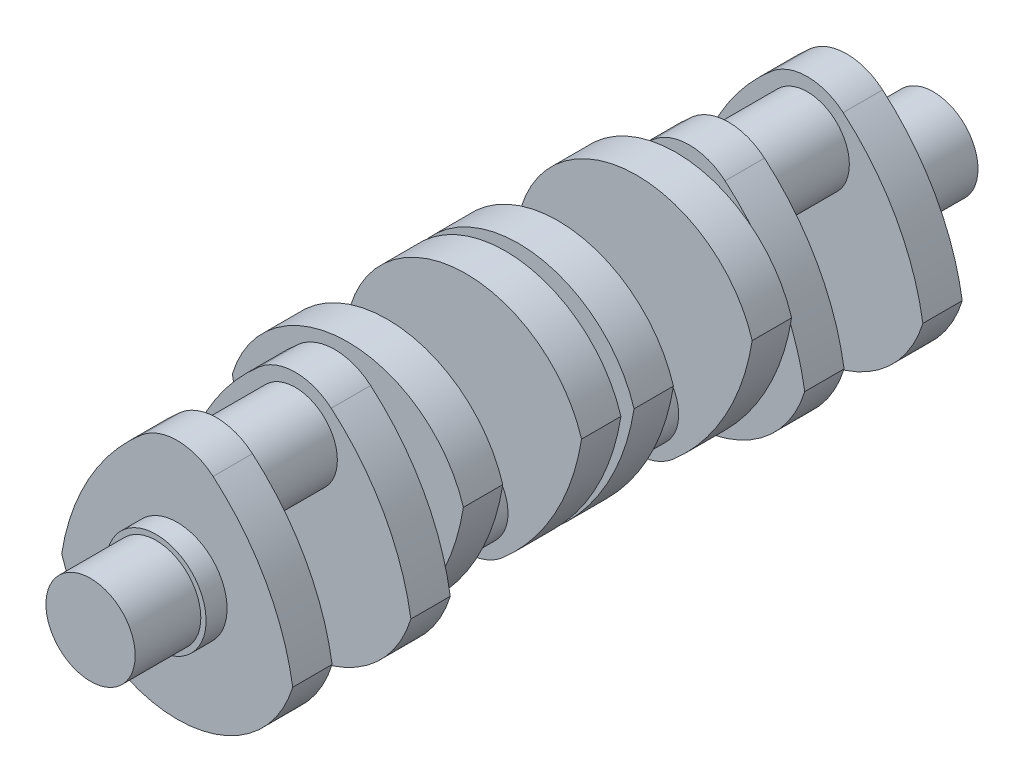
SolidWorks part; units mm, degrees
ref_plane "Front Plane" through (0, 0, 0) normal (0, 0, 1) x (1, 0, 0)
ref_plane "Top Plane" through (0, 0, 0) normal (0, 1, 0) x (1, 0, 0)
ref_plane "Right Plane" through (0, 0, 0) normal (1, 0, 0) x (0, 0, -1)
sketch "Sketch1" plane through (0, 0, 0) normal (0, 0, 1) x (1, 0, 0)
  circle A0 centre (0, 0) radius 19
  circle A1 centre (0, 0) radius 17
  dimension "D1" = 34
  dimension "D2" = 38
extrude "Boss-Extrude1" add sketch "Sketch1" along normal blind 25 contours A1
sketch "Sketch2" plane through (0, 0, 0) normal (0, 0, -1) x (-1, 0, 0)
  circle A0 centre (0, 0) radius 19
  dimension "D1" = 38
extrude "Boss-Extrude2" add sketch "Sketch2" along normal blind 8
sketch "Sketch3" plane through (0, 0, -8) normal (0, 0, -1) x (-1, 0, 0)
  line L1 (-44, -13.4164) -> (44, -13.4164) construction
  line L2 (0, 0) -> (0, -19) construction
  arc A1 (-44, -13.4164) -> (44, -13.4164) centre (0, 0) ccw
  arc A2 (-44, -13.4164) -> (-13.6681, 40.9431) centre (44.9095, -27.3845) cw
  circle A3 centre (0, 0) radius 19 construction
  arc A4 (44, -13.4164) -> (13.6681, 40.9431) centre (-44.9095, -27.3845) ccw
  arc A5 (13.6681, 40.9431) -> (-13.6681, 40.9431) centre (0, 25) ccw
  point P11 (19.2731, 33.3395)
  point P14 (-13.2566, 41.386)
  point P15 (14.4199, 41.386)
  point P16 (0, 0)
  dimension "D1" = 92
  dimension "D2" = 90
  dimension "D4" = 21
  dimension "D3" = 88
  dimension "D5" = 25
extrude "Boss-Extrude3" add sketch "Sketch3" along normal blind 15
sketch "Sketch4" plane through (0, 0, -23) normal (0, 0, -1) x (-1, 0, 0)
  circle A0 centre (0, 25) radius 16
  dimension "D2" = 32
  dimension "D1" = 25
extrude "Boss-Extrude4" add sketch "Sketch4" along normal blind 15
mirror "Mirror2" about plane through (0, 25, -38) normal (0, 0, -1) of "Boss-Extrude3", "Boss-Extrude4"
sketch "Sketch5" plane through (0, 0, -68) normal (0, 0, -1) x (-1, 0, 0)
  circle A0 centre (0, 0) radius 17
  dimension "D1" = 34
extrude "Boss-Extrude5" add sketch "Sketch5" along normal blind 5
sketch "Sketch6" plane through (0, 0, -73) normal (0, 0, -1) x (-1, 0, 0)
  circle A0 centre (0, 0) radius 17 construction
  arc A10 (44, 13.4164) -> (-44, 13.4164) centre (0, 0) ccw
  arc A11 (-44, 13.4164) -> (-13.6681, -40.9431) centre (44.9095, 27.3845) ccw
  arc A12 (-13.6681, -40.9431) -> (13.6681, -40.9431) centre (0, -25) ccw
  arc A13 (13.6681, -40.9431) -> (44, 13.4164) centre (-44.9095, 27.3845) ccw
  dimension "D1" = 46
  dimension "D2" = 90
  dimension "D3" = 21
  dimension "D4" = 13.6681
  dimension "D5" = 44
extrude "Boss-Extrude6" add sketch "Sketch6" along normal blind 15
sketch "Sketch7" plane through (0, 0, -88) normal (0, 0, -1) x (-1, 0, 0)
  circle A0 centre (0, -25) radius 16
  dimension "D1" = 32
  dimension "D2" = 25
extrude "Boss-Extrude7" add sketch "Sketch7" along normal blind 30
sketch "Sketch8" plane through (0, 0, -118) normal (0, 0, -1) x (-1, 0, 0)
  arc A4 (44, 13.4164) -> (-44, 13.4164) centre (0, 0) ccw
  arc A5 (-44, 13.4164) -> (-13.6681, -40.9431) centre (44.9095, 27.3845) ccw
  arc A6 (-13.6681, -40.9431) -> (13.6681, -40.9431) centre (0, -25) ccw
  arc A7 (13.6681, -40.9431) -> (44, 13.4164) centre (-44.9095, 27.3845) ccw
  arc A8 (44, 13.4164) -> (-44, 13.4164) centre (0, 0) ccw
  arc A9 (-44, 13.4164) -> (-13.6681, -40.9431) centre (44.9095, 27.3845) ccw
  arc A10 (-13.6681, -40.9431) -> (13.6681, -40.9431) centre (0, -25) ccw
  arc A11 (13.6681, -40.9431) -> (44, 13.4164) centre (-44.9095, 27.3845) ccw
  dimension "D1" = 0
extrude "Boss-Extrude8" add sketch "Sketch8" along normal blind 15
sketch "Sketch9" plane through (0, 0, -133) normal (0, 0, -1) x (-1, 0, 0)
  circle A0 centre (0, 0) radius 17
  dimension "D1" = 34
extrude "Boss-Extrude9" add sketch "Sketch9" along normal blind 2.5
mirror "Mirror3" about plane through (0, 0, -135.5) normal (0, 0, -1) of bodies 111
